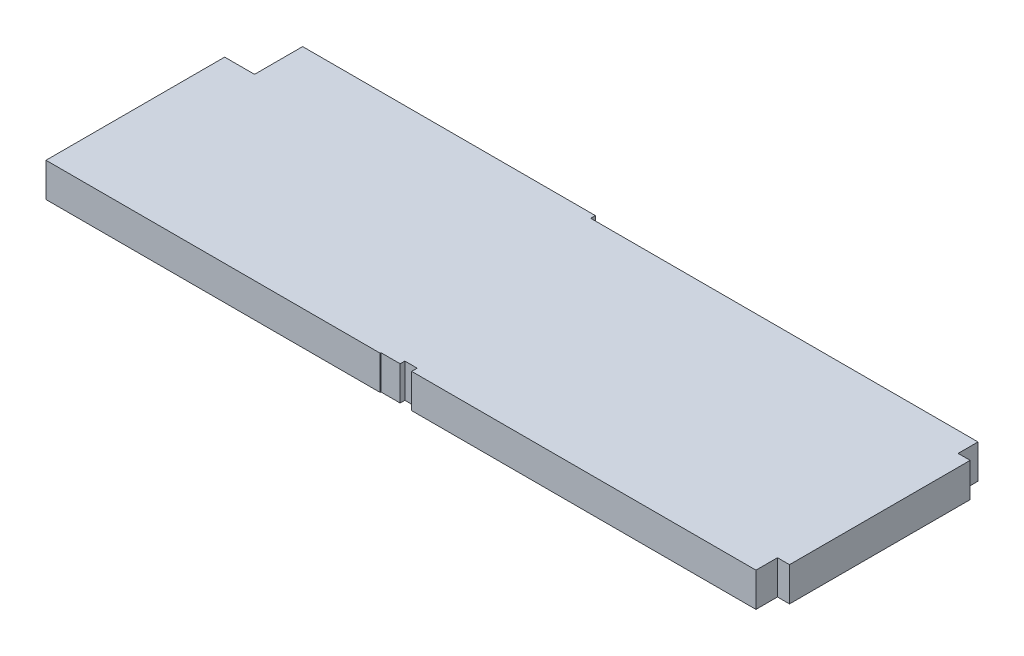
SolidWorks part; units mm, degrees
ref_plane "Front Plane" through (0, 0, 0) normal (0, 0, 1) x (1, 0, 0)
ref_plane "Top Plane" through (0, 0, 0) normal (0, 1, 0) x (1, 0, 0)
ref_plane "Right Plane" through (0, 0, 0) normal (1, 0, 0) x (0, 0, -1)
sketch "Sketch1" plane through (0, 0, 0) normal (0, 1, 0) x (1, 0, 0)
  line L0 (0, 0) -> (0, 75.95)
  line L1 (0, 75.95) -> (12.7, 75.95)
  line L2 (12.7, 75.95) -> (12.7, 96.4)
  line L3 (12.7, 96.4) -> (137.15, 96.4)
  line L4 (137.15, 96.4) -> (137.15, 94.4)
  line L5 (137.15, 94.4) -> (301.8, 94.4)
  line L6 (306.92, 9.15) -> (306.92, 85.95)
  line L7 (301.8, 0) -> (155.45, 0)
  line L8 (155.45, 0) -> (155.45, 2.35)
  line L9 (155.45, 2.35) -> (150.2, 2.35)
  line L10 (150.2, 2.35) -> (150.2, 0.35)
  line L11 (150.2, 0.35) -> (142.05, 0.35)
  line L12 (142.05, 0.35) -> (142.05, 0)
  line L13 (142.05, 0) -> (0, 0)
  line L14 (301.8, 94.4) -> (301.8, 85.95)
  line L15 (301.8, 85.95) -> (306.92, 85.95)
  line L16 (306.92, 9.15) -> (301.8, 9.15)
  line L17 (301.8, 9.15) -> (301.8, 0)
  line L18 (301.8, 85.95) -> (301.8, 9.15) construction
  dimension "D1" = 2
  dimension "D2" = 306.92
  dimension "D3" = 2.35
  dimension "D4" = 5.25
  dimension "D5" = 13.4
  dimension "D6" = 0.35
  dimension "D7" = 142.05
  dimension "D8" = 75.95
  dimension "D9" = 12.7
  dimension "D10" = 137.15
  dimension "D11" = 96.4
  dimension "D12" = 8.45
  dimension "D13" = 9.15
  dimension "D14" = 5.12
extrude "Boss-Extrude1" add sketch "Sketch1" along normal blind 14.47
